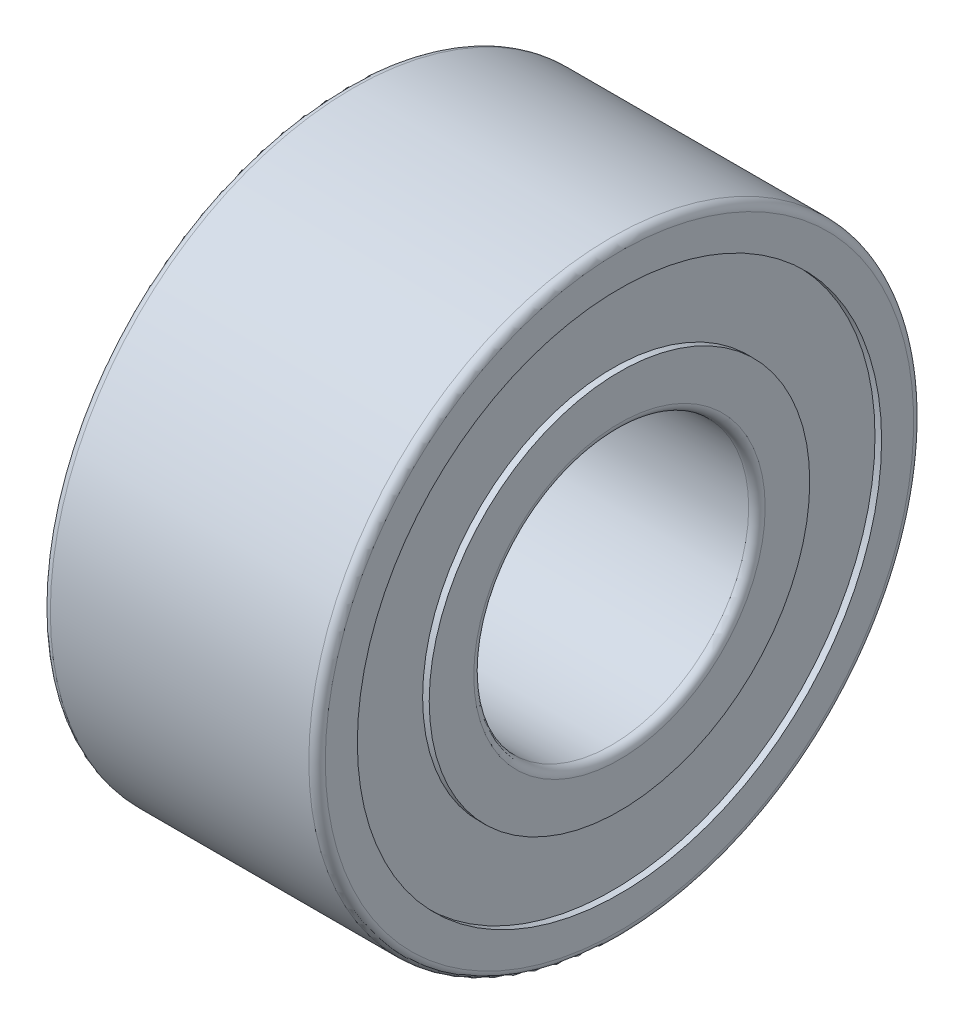
SolidWorks part; units mm, degrees
ref_plane "Front Plane" through (0, 0, 0) normal (0, 0, 1) x (1, 0, 0)
ref_plane "Top Plane" through (0, 0, 0) normal (0, 1, 0) x (1, 0, 0)
ref_plane "Right Plane" through (0, 0, 0) normal (1, 0, 0) x (0, 0, -1)
ref_plane "Plane1" through (0, 0, 0) normal (0, 0, 1) x (1, 0, 0)
sketch "Sketch1" plane through (0, 0, 0) normal (0, 0, 1) x (1, 0, 0)
  line L0 (0, 5.35) -> (0, 4.767)
  line L1 (0, 4.767) -> (0.12, 4.767)
  line L2 (0.12, 4.767) -> (0.12, 3.46)
  line L3 (0.12, 3.46) -> (0, 3.46)
  line L4 (0, 3.46) -> (0, 2.65)
  line L5 (0.15, 2.5) -> (4.85, 2.5)
  line L6 (5, 2.65) -> (5, 3.46)
  line L7 (5, 3.46) -> (4.88, 3.46)
  line L8 (4.88, 3.46) -> (4.88, 4.767)
  line L9 (4.88, 4.767) -> (5, 4.767)
  line L10 (5, 4.767) -> (5, 5.35)
  line L11 (4.85, 5.5) -> (0.15, 5.5)
  line L12 (4.85, 0) -> (0.15, 0) construction
  arc A0 (0, 2.65) -> (0.15, 2.5) centre (0.15, 2.65) ccw
  arc A1 (4.85, 2.5) -> (5, 2.65) centre (4.85, 2.65) ccw
  arc A2 (5, 5.35) -> (4.85, 5.5) centre (4.85, 5.35) ccw
  arc A3 (0.15, 5.5) -> (0, 5.35) centre (0.15, 5.35) ccw
revolve "Revolve1" add sketch "Sketch1" angle 360 about L12
